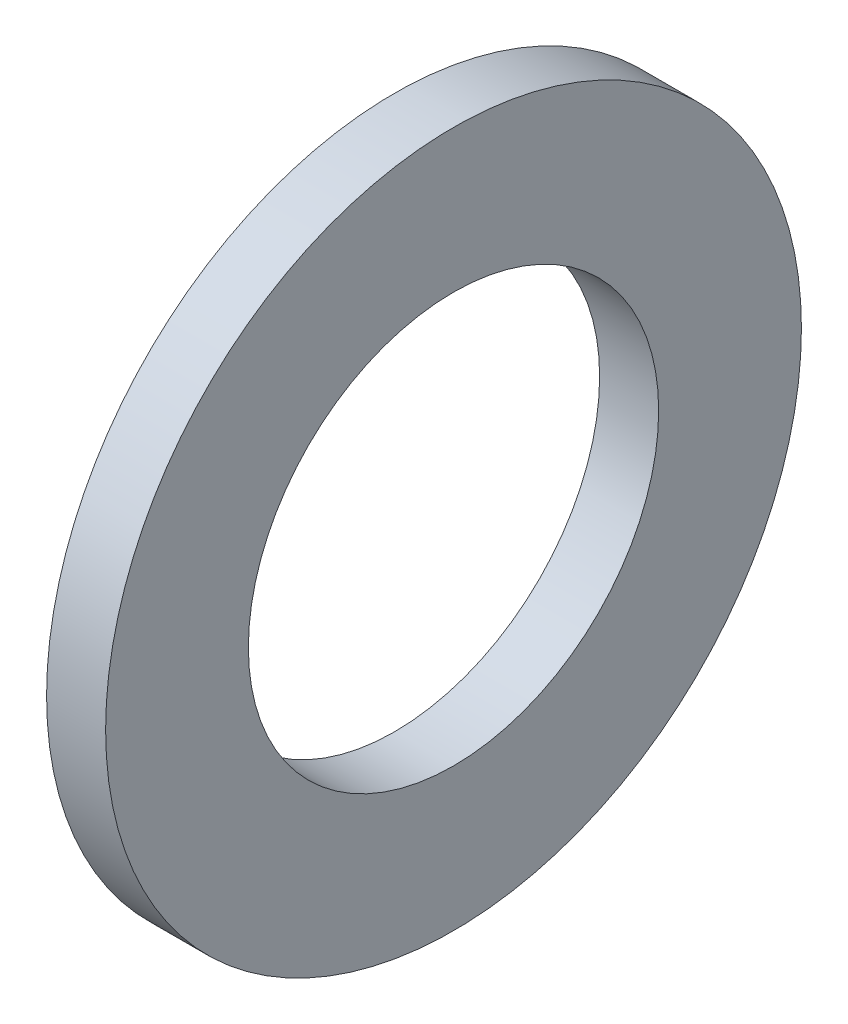
SolidWorks part; units mm, degrees
ref_plane "Plane1" through (0, 0, 0) normal (0, 0, 1) x (1, 0, 0)
ref_plane "Plane2" through (0, 0, 0) normal (0, 1, 0) x (1, 0, 0)
ref_plane "Plane3" through (0, 0, 0) normal (1, 0, 0) x (0, 0, -1)
other "Configuration Table"
sketch "Sketch1" plane through (0, 0, 0) normal (0, 0, 1) x (1, 0, 0)
  line L0 (-34.925, 0) -> (9.525, 0) construction
  line L1 (0, 19.46) -> (0, 33)
  line L2 (0, 33) -> (-5.6, 33)
  line L3 (-5.6, 33) -> (-5.6, 19.46)
  line L4 (-5.6, 19.46) -> (0, 19.46)
  dimension "Thickness" = 5.6
  dimension "Inside_dia" = 38.92
  dimension "Outside_dia" = 66
revolve "Base-Revolve" add sketch "Sketch1" angle 360 about L0
